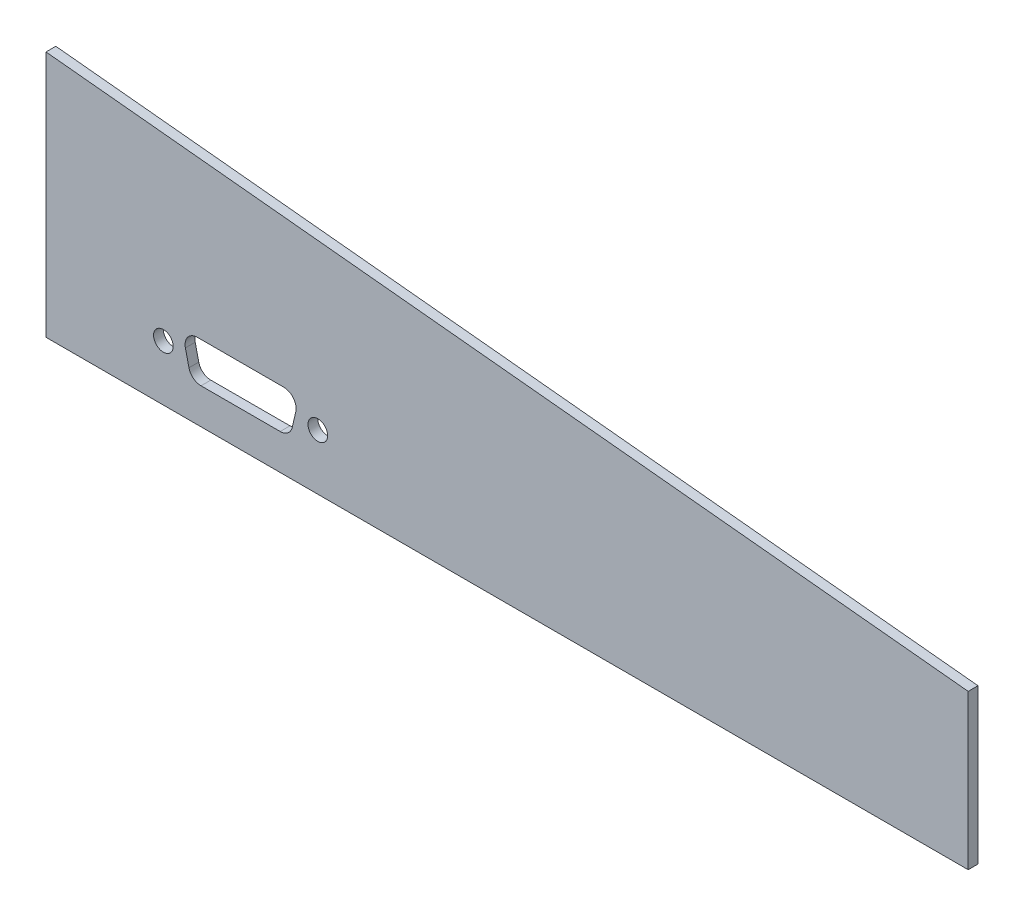
SolidWorks part; units mm, degrees
ref_plane "Plan de face" through (0, 0, 0) normal (0, 0, 1) x (1, 0, 0)
ref_plane "Plan de dessus" through (0, 0, 0) normal (0, 1, 0) x (1, 0, 0)
ref_plane "Plan de droite" through (0, 0, 0) normal (1, 0, 0) x (0, 0, -1)
sketch "Esquisse1" plane through (0, 0, 0) normal (0, 0, 1) x (1, 0, 0)
  line L0 (-149.2481, 40) -> (-149.2481, 0)
  line L1 (-149.2481, 0) -> (0, 0)
  line L2 (0, 0) -> (0, 25)
  line L3 (0, 25) -> (-149.2481, 40)
  line L4 (-127.2531, 12.25) -> (-108.2531, 12.25)
  line L5 (-108.2531, 12.25) -> (-109.7531, 5.75)
  line L6 (-109.7531, 5.75) -> (-125.7531, 5.75)
  line L7 (-125.7531, 5.75) -> (-127.2531, 12.25)
  line L8 (-130.2481, 9) -> (-105.2581, 9) construction
  circle A0 centre (-130.2481, 9) radius 1.59
  circle A1 centre (-105.2581, 9) radius 1.59
  point P10 (-117.7531, 5.75)
  point P11 (-117.7531, 12.25)
  point P15 (-47.1889, 14.5486)
  point P16 (-109.0031, 9)
  point P17 (-46.6632, 14.4629)
  point P18 (-117.7531, 9)
  dimension "D7" = 3.18
  dimension "D1" = 25
  dimension "D2" = 40
  dimension "D3" = 150
  dimension "D4" = 19
  dimension "D5" = 16
  dimension "D6" = 6.5
  dimension "D8" = 24.99
  dimension "D9" = 19
  dimension "D10" = 9
extrude "Boss.-Extru.1" add sketch "Esquisse1" along normal blind 1.5875
fillet "Congé1" radius 2 4 edges at (-108.2531, 12.25, 0.7937) (-109.7531, 5.75, 0.7937) (-127.2531, 12.25, 0.7937) (-125.7531, 5.75, 0.7937)
